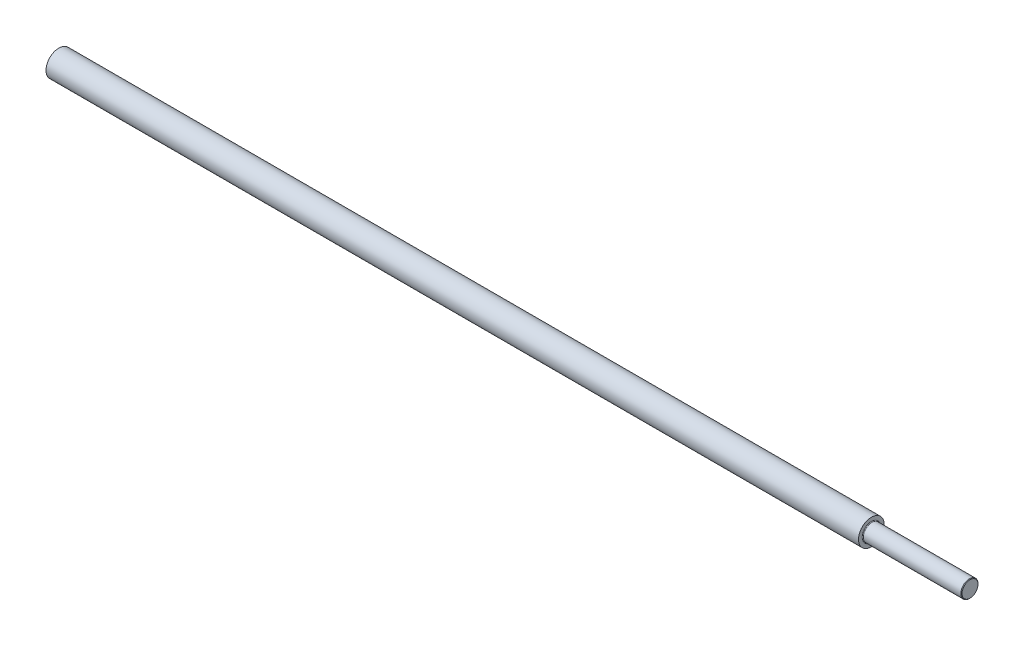
SolidWorks part; units mm, degrees
ref_plane "Front Plane" through (0, 0, 0) normal (0, 0, 1) x (1, 0, 0)
ref_plane "Top Plane" through (0, 0, 0) normal (0, 1, 0) x (1, 0, 0)
ref_plane "Right Plane" through (0, 0, 0) normal (1, 0, 0) x (0, 0, -1)
ref_plane "Plane1" through (0, 0, 0) normal (0, 0, 1) x (1, 0, 0)
sketch "Sketch1" plane through (0, 0, 0) normal (0, 0, 1) x (1, 0, 0)
  line L0 (0, 0) -> (0, 6)
  line L1 (0, 6) -> (379, 6)
  line L2 (379, 6) -> (379, 4.3)
  line L3 (379.3, 4) -> (424.7333, 4)
  line L4 (424.7333, 4) -> (425, 3.7333)
  line L5 (425, 3.7333) -> (425, 0)
  line L6 (425, 0) -> (0, 0)
  line L7 (425, 0) -> (0, 0) construction
  arc A0 (379, 4.3) -> (379.3, 4) centre (379.3, 4.3) ccw
  dimension "D7" = 0.3
  dimension "D1" = 425
  dimension "D2" = 46
  dimension "D3" = 6
  dimension "D4" = 4
  dimension "D5" = 0.2667
  dimension "D6" = 135
revolve "Revolve1" add sketch "Sketch1" angle 360 about L7
cosmetic thread "Cosmetic Thread1" parameters "D1"=370, "D2"=9.5
